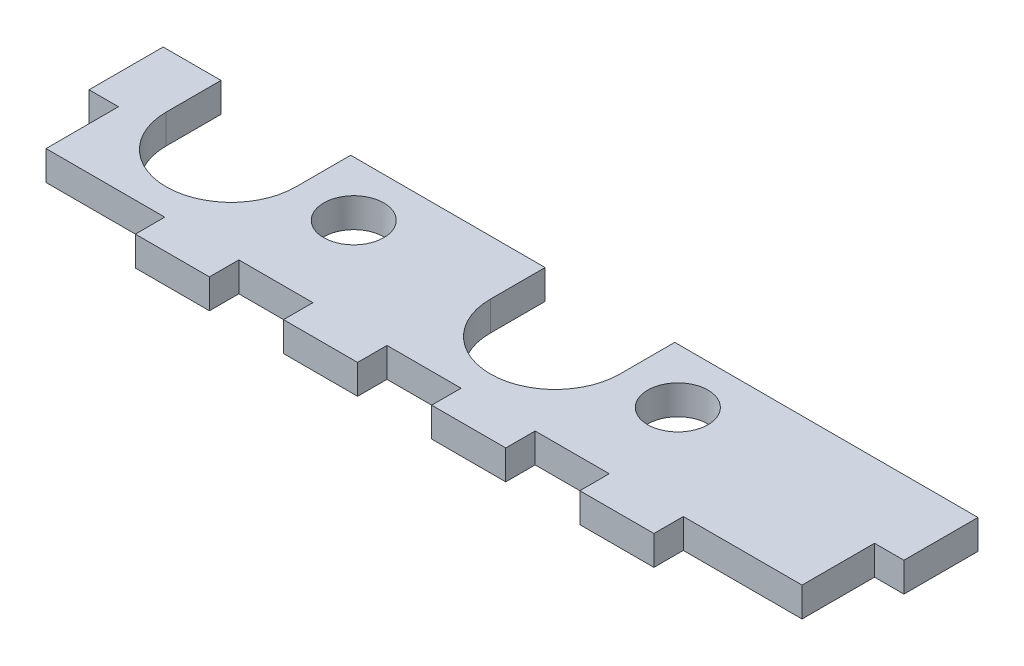
SolidWorks part; units mm, degrees
ref_plane "Front Plane" through (0, 0, 0) normal (0, 0, 1) x (1, 0, 0)
ref_plane "Top Plane" through (0, 0, 0) normal (0, 1, 0) x (1, 0, 0)
ref_plane "Right Plane" through (0, 0, 0) normal (1, 0, 0) x (0, 0, -1)
sketch "Sketch3" plane through (0, 0, 0) normal (0, 1, 0) x (1, 0, 0)
  line L1 (0, 0) -> (88, 0)
  line L2 (0, 0) -> (0, -30)
  line L3 (0, -30) -> (88, -30)
  line L4 (88, 0) -> (88, -30)
  dimension "D1" = 30
  dimension "D2" = 88
extrude "Boss-Extrude1" add sketch "Sketch3" along normal blind 3.175
sketch "Sketch4" plane through (0, 3.175, 0) normal (0, 1, 0) x (1, 0, 0)
  line L0 (44, 0) -> (44, -30) construction
  line L1 (88, 0) -> (0, 0) construction
  line L2 (0, -30) -> (88, -30) construction
  line L3 (0, -15) -> (88, -15) construction
  line L4 (0, 0) -> (0, -30) construction
  line L5 (88, -30) -> (88, 0) construction
  line L6 (16, -30) -> (16, -26.825)
  line L7 (40, -30) -> (48, -30)
  line L8 (0, -26.825) -> (16, -26.825)
  line L9 (40, -26.825) -> (48, -26.825)
  line L10 (48, -30) -> (48, -26.825)
  line L11 (56, -30) -> (64, -30)
  line L12 (56, -30) -> (56, -26.825)
  line L13 (56, -26.825) -> (64, -26.825)
  line L14 (64, -30) -> (64, -26.825)
  line L15 (88, -30) -> (72, -30)
  line L16 (88, -30) -> (88, -26.825)
  line L17 (88, -26.825) -> (72, -26.825)
  line L18 (72, -30) -> (72, -26.825)
  line L19 (0, -30) -> (0, -26.825)
  line L20 (0, -30) -> (16, -30)
  line L21 (24, -30) -> (24, -26.825)
  line L22 (32, -26.825) -> (24, -26.825)
  line L23 (32, -30) -> (32, -26.825)
  line L24 (32, -30) -> (24, -30)
  line L25 (40, -30) -> (40, -26.825)
  line L26 (88, -19) -> (88, -26.825)
  line L27 (0, 0) -> (3.175, 0)
  line L28 (0, 0) -> (0, -11)
  line L29 (0, -11) -> (3.175, -11)
  line L30 (3.175, 0) -> (3.175, -11)
  line L31 (84.825, -19) -> (84.825, -26.825)
  line L32 (88, -19) -> (84.825, -19)
  line L33 (84.825, 0) -> (84.825, -11)
  line L34 (88, -11) -> (84.825, -11)
  line L35 (0, -19) -> (3.175, -19)
  line L36 (0, -19) -> (0, -26.825)
  line L37 (0, -26.825) -> (3.175, -26.825)
  line L38 (3.175, -19) -> (3.175, -26.825)
  line L39 (88, 0) -> (88, -11)
  line L40 (88, 0) -> (84.825, 0)
  line L41 (84.825, -26.825) -> (88, -26.825)
  line L42 (88, -19) -> (88, -26.825)
  point P34 (44, -26.825)
  line M11 (0, 0) -> (0, -30)
  line M12 (0, -30) -> (88, -30)
  line M13 (88, -30) -> (88, 0)
  line M14 (88, 0) -> (0, 0)
  dimension "D1" = 4
  dimension "D2" = 3.175
  dimension "D3" = 8
  dimension "D4" = 3.175
  dimension "D5" = 8
  dimension "D6" = 3.175
  dimension "D7" = 8
  dimension "D8" = 8
extrude "Cut-Extrude1" cut sketch "Sketch4" against normal up to next contours L38 L35 L8 M11 | L8 L6 M11 M12 | L23 L22 L21 M12 | L25 L10 L9 M12 | L14 L13 L12 M12 | L32 L31 L17 M13 | L34 L33 M13 M14 | L18 L17 M12 M13 | L30 L29 M14 M11
sketch "Sketch5" plane through (0, 3.175, 0) normal (0, 1, 0) x (1, 0, 0)
  line L0 (0, -16.915) -> (88, -16.915) construction
  line L1 (0, -11) -> (0, -19) construction
  line L2 (88, -19) -> (88, -11) construction
  line L3 (32, -26.825) -> (24, -26.825) construction
  line L4 (44, 0) -> (44, -26.825) construction
  line L5 (84.825, 0) -> (3.175, 0) construction
  line L6 (40, -26.825) -> (48, -26.825) construction
  circle A0 centre (61.5, -16.915) radius 3.25
  circle A1 centre (26.5, -16.915) radius 3.25
  point P16 (44, -16.915)
  dimension "D2" = 6.5
  dimension "D1" = 9.91
  dimension "D3" = 17.5
extrude "Cut-Extrude2" cut sketch "Sketch5" against normal up to next
sketch "Sketch6" plane through (0, 3.175, 0) normal (0, 1, 0) x (1, 0, 0)
  line L1 (3.175, -11) -> (84.825, -11)
  line L2 (3.175, -11) -> (3.175, 0)
  line L3 (3.175, 0) -> (84.825, 0)
  line L4 (84.825, -11) -> (84.825, 0)
extrude "Cut-Extrude3" cut sketch "Sketch6" against normal up to next
sketch "Sketch7" plane through (0, 3.175, 0) normal (0, 1, 0) x (1, 0, 0)
  line L0 (44, -11) -> (44, -26.825) construction
  line L1 (88, -11) -> (0, -11) construction
  line L2 (40, -26.825) -> (48, -26.825) construction
  line L3 (0, -16.915) -> (88, -16.915) construction
  line L4 (0, -11) -> (0, -19) construction
  line L5 (88, -19) -> (88, -11) construction
  line L6 (6.25, -16.915) -> (6.25, -11)
  line L7 (20.25, -16.915) -> (20.25, -11)
  line L8 (26.5, -13.665) -> (26.5, -20.165) construction
  line L9 (41.25, -16.915) -> (41.25, -11)
  line L10 (55.25, -16.915) -> (55.25, -11)
  line L11 (6.25, -11) -> (20.25, -11)
  line L12 (41.25, -11) -> (55.25, -11)
  line L13 (61.5, -13.665) -> (61.5, -20.165) construction
  circle A0 centre (26.5, -16.915) radius 3.25 construction
  arc A2 (6.25, -16.915) -> (20.25, -16.915) centre (13.25, -16.915) ccw
  arc A3 (41.25, -16.915) -> (55.25, -16.915) centre (48.25, -16.915) ccw
  point P15 (13.25, -16.915)
  point P16 (6.25, -16.915)
  point P28 (48.25, -16.915)
  point P29 (41.25, -16.915)
  dimension "D1" = 13.25
  dimension "D2" = 7
  dimension "D3" = 2
extrude "Cut-Extrude4" cut sketch "Sketch7" against normal up to next
